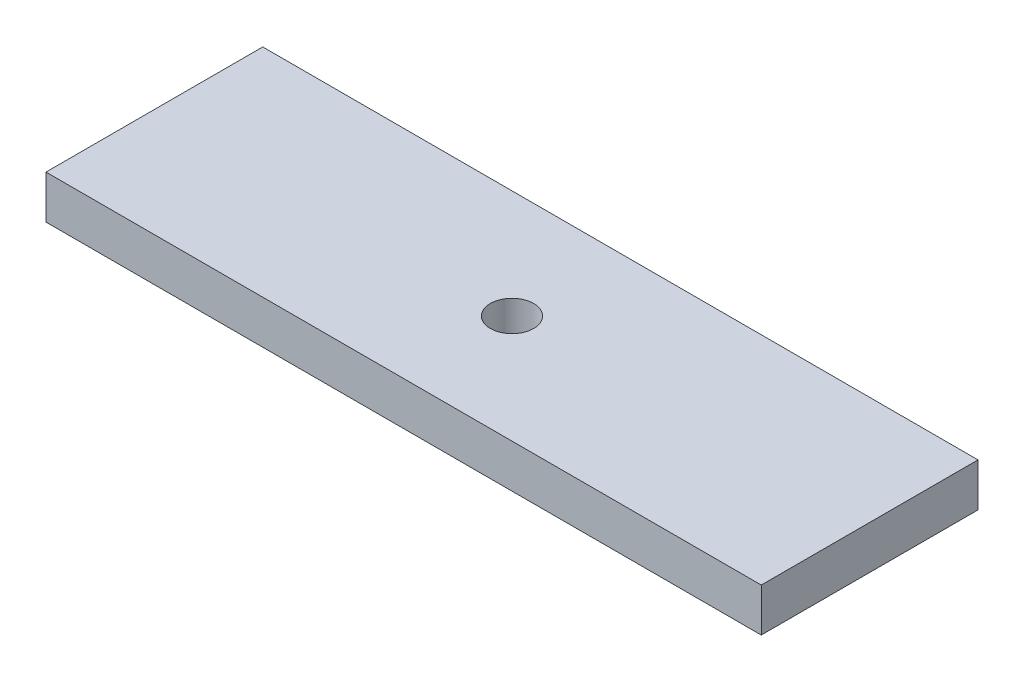
SolidWorks part; units mm, degrees
ref_plane "Front Plane" through (0, 0, 0) normal (0, 0, 1) x (1, 0, 0)
ref_plane "Top Plane" through (0, 0, 0) normal (0, 1, 0) x (1, 0, 0)
ref_plane "Right Plane" through (0, 0, 0) normal (1, 0, 0) x (0, 0, -1)
sketch "Sketch1" plane through (0, 0, 0) normal (0, 1, 0) x (1, 0, 0)
  line L1 (0, 0) -> (66, 0)
  line L2 (0, 0) -> (0, -20)
  line L3 (0, -20) -> (66, -20)
  line L4 (66, 0) -> (66, -20)
  dimension "D1" = 66
  dimension "D2" = 20
extrude "Boss-Extrude1" add sketch "Sketch1" along normal blind 4
sketch "Sketch2" plane through (0, 4, 0) normal (0, 1, 0) x (1, 0, 0)
  line L0 (0, -10) -> (66, -10) construction
  line L1 (0, 0) -> (0, -20) construction
  line L2 (66, -20) -> (66, 0) construction
  circle A1 centre (33, -10) radius 2
  point P6 (0, 0)
  dimension "D1" = 4
extrude "Cut-Extrude1" cut sketch "Sketch2" against normal through all
